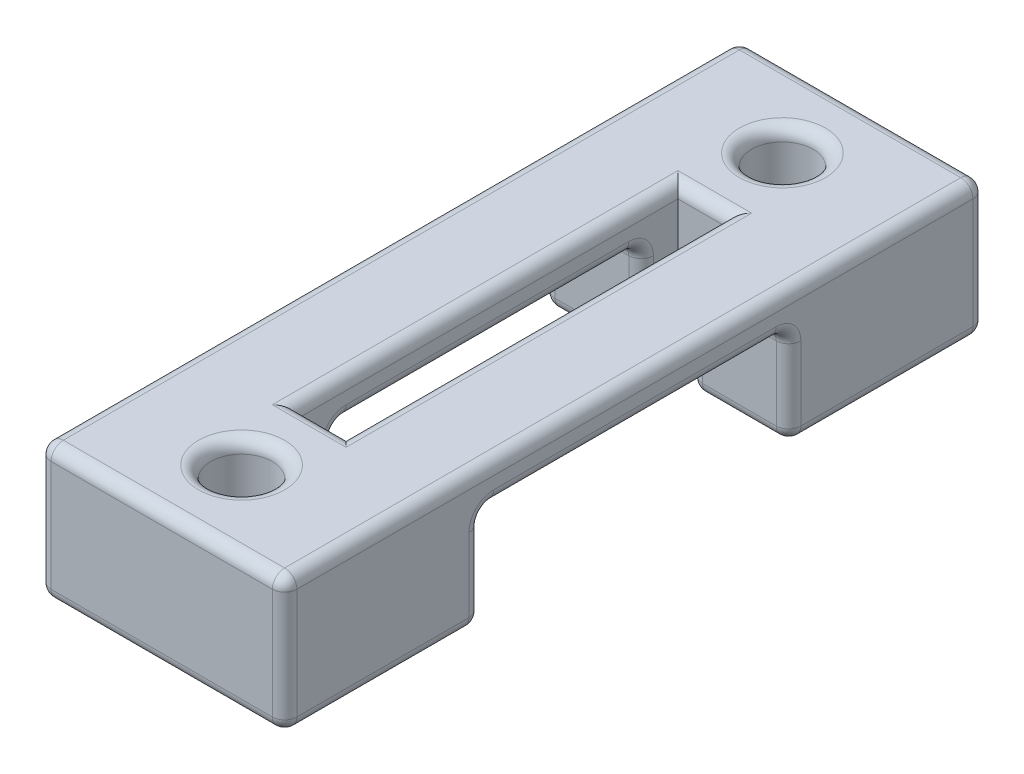
SolidWorks part; units mm, degrees
ref_plane "Front Plane" through (0, 0, 0) normal (0, 0, 1) x (1, 0, 0)
ref_plane "Top Plane" through (0, 0, 0) normal (0, 1, 0) x (1, 0, 0)
ref_plane "Right Plane" through (0, 0, 0) normal (1, 0, 0) x (0, 0, -1)
sketch "Sketch1" plane through (0, 0, 0) normal (1, 0, 0) x (0, 0, -1)
  line L0 (-14.25, 0) -> (-6.25, 0)
  line L1 (-6.25, 0) -> (-6.25, 4)
  line L2 (6.25, 4) -> (-6.25, 4)
  line L3 (6.25, 4) -> (6.25, 0)
  line L4 (14.25, 0) -> (6.25, 0)
  line L5 (14.25, 0) -> (14.25, 5.5)
  line L6 (14.25, 5.5) -> (-14.25, 5.5)
  line L7 (-14.25, 5.5) -> (-14.25, 0)
  point P7 (0, 4)
  point P10 (0, 5.5)
  dimension "D1" = 12.5
  dimension "D2" = 4
  dimension "D3" = 4
  dimension "D4" = 1.5
  dimension "D5" = 8
extrude "Boss-Extrude1" add sketch "Sketch1" along normal blind 10
sketch "Sketch2" plane through (0, 5.5, 0) normal (0, 1, 0) x (1, 0, 0)
  line L0 (0, 0) -> (10, 0) construction
  line L1 (10, 14.25) -> (10, -14.25) construction
  line L2 (4, -7.75) -> (6, -7.75)
  line L3 (4, -7.75) -> (4, 7.75)
  line L4 (6, -7.75) -> (6, 7.75)
  line L5 (4, 7.75) -> (6, 7.75)
  line L6 (4, -7.75) -> (6, 7.75) construction
  line L7 (6, -7.75) -> (4, 7.75) construction
  point P5 (5, 0)
  point P6 (5, 0)
  dimension "D1" = 2
  dimension "D2" = 15.5
extrude "Cut-Extrude1" cut sketch "Sketch2" against normal blind 10
sketch "Sketch3" plane through (0, 0, 0) normal (0, -1, 0) x (1, 0, 0)
  line L0 (0, 0) -> (10, 0) construction
  line L1 (10, 6.25) -> (10, -6.25) construction
  line L2 (5, -11) -> (5, 11) construction
  circle A0 centre (5, 11) radius 1.25
  circle A1 centre (5, -11) radius 1.25
  point P8 (5, 0)
  dimension "D2" = 2.5
  dimension "D3" = 2.5
  dimension "D1" = 22
extrude "Cut-Extrude2" cut sketch "Sketch3" against normal blind 10
fillet "Fillet1" radius 0.5 48 edges at (0, 2, 6.25) (0, 4, 0) (0, 2, -6.25) (0, 2.75, 14.25) (0, 2.75, -14.25) (10, 2.75, -14.25) (10, 2, -6.25) (10, 4, 0) (10, 2, 6.25) (10, 2.75, 14.25) (5, 5.5, -14.25) (10, 5.5, 0) (5, 5.5, 14.25) (0, 5.5, 0) (6, 5.5, 0) (5, 5.5, -7.75) (4, 5.5, 0) (5, 5.5, 7.75) (5, 5.5, -12.25) (5, 5.5, 9.75) (6, 0, -7) (8, 0, -6.25) (10, 0, -10.25) (5, 0, -14.25) (0, 0, -10.25) (2, 0, -6.25) (4, 0, -7) (5, 0, -7.75) (5, 0, -12.25) (0, 0, 10.25) (5, 0, 14.25) (10, 0, 10.25) (8, 0, 6.25) (6, 0, 7) (5, 0, 7.75) (4, 0, 7) (2, 0, 6.25) (5, 0, 9.75) (2, 4, 6.25) (8, 4, 6.25) (8, 4, -6.25) (2, 4, -6.25) (6, 4, 0) (4, 4, 0) (4, 2, 6.25) (6, 2, 6.25) (6, 2, -6.25) (4, 2, -6.25)
